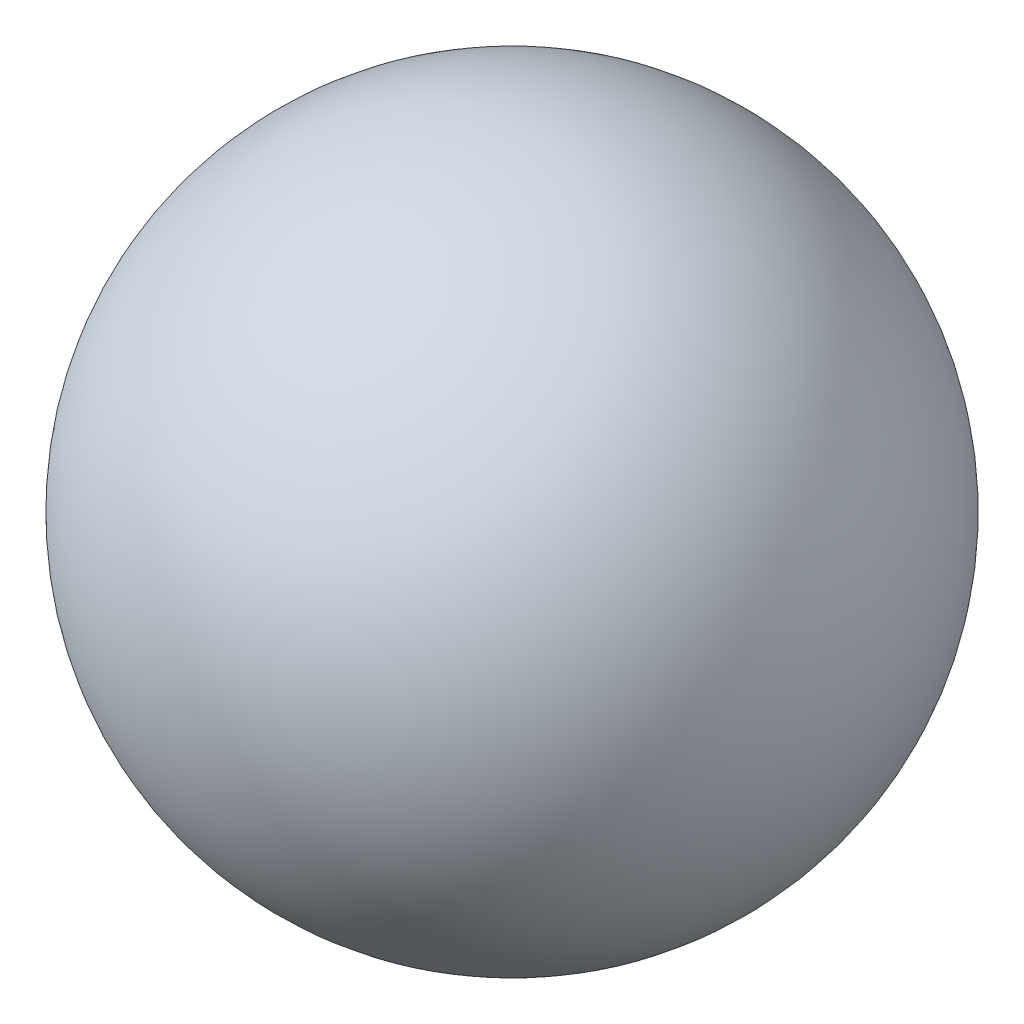
SolidWorks part; units mm, degrees
material "6061-T4 (SS)"
ref_plane "Front Plane" through (0, 0, 0) normal (0, 0, 1) x (1, 0, 0)
ref_plane "Top Plane" through (0, 0, 0) normal (0, 1, 0) x (1, 0, 0)
ref_plane "Right Plane" through (0, 0, 0) normal (1, 0, 0) x (0, 0, -1)
sketch "Sketch2" plane through (0, 0, 0) normal (0, 0, 1) x (1, 0, 0)
  line L0 (0, 367.6) -> (0, -367.6)
  arc A4 (0, 367.6) -> (0, -367.6) centre (0, 0) cw
  dimension "D2" = 367.6
revolve "Revolve7" add sketch "Sketch2" angle 360 about L0
